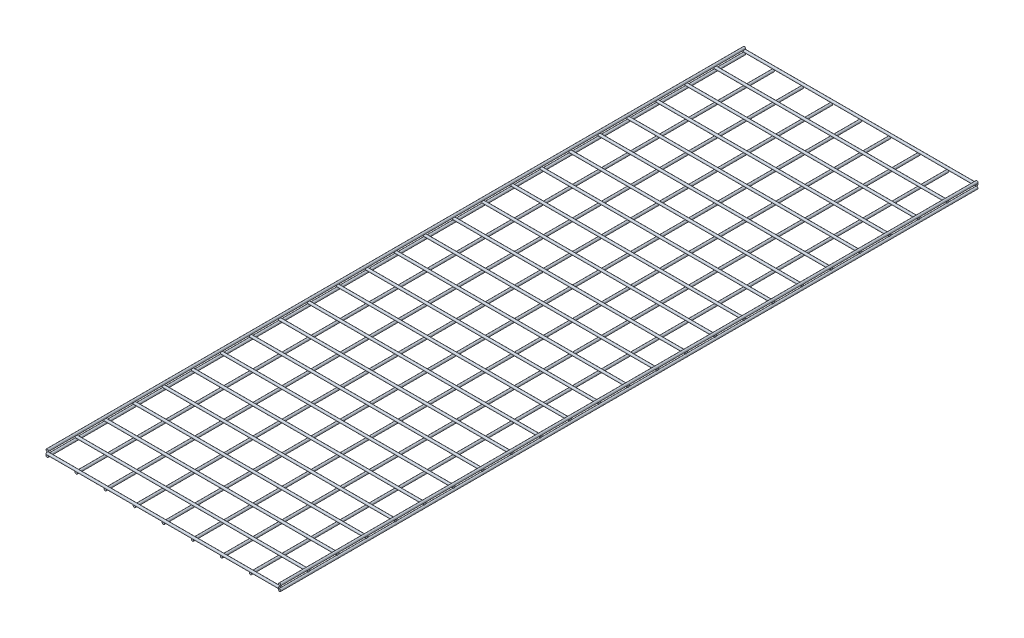
SolidWorks part; units mm, degrees
material "Plain Carbon Steel"
ref_plane "Front Plane" through (0, 0, 0) normal (0, 0, 1) x (1, 0, 0)
ref_plane "Top Plane" through (0, 0, 0) normal (0, 1, 0) x (1, 0, 0)
ref_plane "Right Plane" through (0, 0, 0) normal (1, 0, 0) x (0, 0, -1)
sketch "Sketch1" plane through (0, 0, 0) normal (0, 0, 1) x (1, 0, 0)
  line L0 (0, -55) -> (0, 55) construction
  circle A0 centre (0, 0) radius 3.175
  circle A1 centre (0, 12.7) radius 3.175
  circle A2 centre (76.2, 0) radius 3.175
  circle A3 centre (152.4, 0) radius 3.175
  circle A4 centre (228.6, 0) radius 3.175
  circle A5 centre (304.8, 0) radius 3.175
  circle A6 centre (381, 0) radius 3.175
  circle A7 centre (457.2, 0) radius 3.175
  circle A8 centre (533.4, 0) radius 3.175
  circle A9 centre (609.6, 0) radius 3.175
  circle A10 centre (609.6, 12.7) radius 3.175
  dimension "D1" = 6.35
  dimension "D2" = 6.35
  dimension "D6" = 6.35
  dimension "D3" = 12.7
  dimension "D5" = 12.7
  dimension "D7" = 76.2
  dimension "D4" = 9
extrude "Boss-Extrude1" add sketch "Sketch1" along normal blind 1828.8
sketch "Sketch2" plane through (0, 0, 0) normal (1, 0, 0) x (0, 0, -1)
  line L0 (0, 15.875) -> (-1828.8, 15.875) construction
  line L1 (0, 10.4775) -> (0, -10.4775) construction
  circle A0 centre (0, 6.35) radius 3.175
  circle A1 centre (-76.2, 6.35) radius 3.175
  circle A2 centre (-152.4, 6.35) radius 3.175
  circle A3 centre (-228.6, 6.35) radius 3.175
  circle A4 centre (-304.8, 6.35) radius 3.175
  circle A5 centre (-381, 6.35) radius 3.175
  circle A6 centre (-457.2, 6.35) radius 3.175
  circle A7 centre (-533.4, 6.35) radius 3.175
  circle A8 centre (-609.6, 6.35) radius 3.175
  circle A9 centre (-685.8, 6.35) radius 3.175
  circle A10 centre (-762, 6.35) radius 3.175
  circle A11 centre (-838.2, 6.35) radius 3.175
  circle A12 centre (-914.4, 6.35) radius 3.175
  circle A13 centre (-990.6, 6.35) radius 3.175
  circle A14 centre (-1066.8, 6.35) radius 3.175
  circle A15 centre (-1143, 6.35) radius 3.175
  circle A16 centre (-1219.2, 6.35) radius 3.175
  circle A17 centre (-1295.4, 6.35) radius 3.175
  circle A18 centre (-1371.6, 6.35) radius 3.175
  circle A19 centre (-1447.8, 6.35) radius 3.175
  circle A20 centre (-1524, 6.35) radius 3.175
  circle A21 centre (-1600.2, 6.35) radius 3.175
  circle A22 centre (-1676.4, 6.35) radius 3.175
  circle A23 centre (-1752.6, 6.35) radius 3.175
  circle A24 centre (-1828.8, 6.35) radius 3.175
  dimension "D2" = 6.35
  dimension "D1" = 9.525
  dimension "D3" = 0
  dimension "D5" = 76.2
  dimension "D4" = 25
extrude "Boss-Extrude2" add sketch "Sketch2" along normal blind 609.6 separate body
ref_plane "Plane1" through (304.8, 0, 0) normal (1, 0, 0) x (0, 0, -1)
ref_plane "Plane2" through (0, 0, 762) normal (0, 0, 1) x (1, 0, 0)
